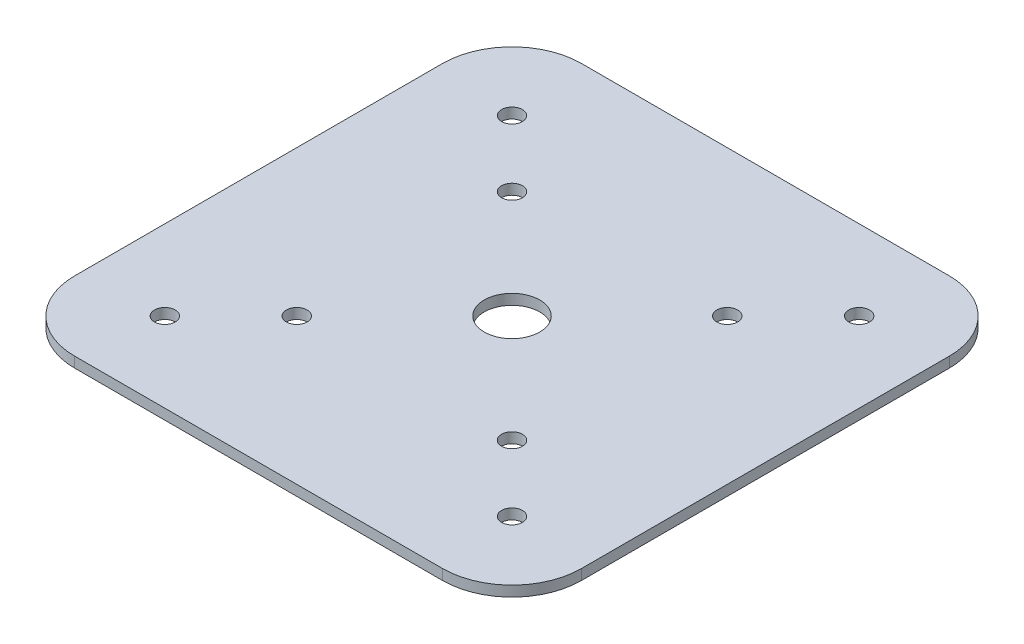
SolidWorks part; units mm, degrees
material "5052-H32"
ref_plane "Front Plane" through (0, 0, 0) normal (0, 0, 1) x (1, 0, 0)
ref_plane "Top Plane" through (0, 0, 0) normal (0, 1, 0) x (1, 0, 0)
ref_plane "Right Plane" through (0, 0, 0) normal (1, 0, 0) x (0, 0, -1)
sketch "Sketch2" plane through (0, 0, 0) normal (0, 1, 0) x (1, 0, 0)
  line L1 (-36.5, 36.5) -> (36.5, 36.5)
  line L2 (-36.5, 36.5) -> (-36.5, -36.5)
  line L3 (-36.5, -36.5) -> (36.5, -36.5)
  line L4 (36.5, 36.5) -> (36.5, -36.5)
  line L5 (-36.5, 36.5) -> (36.5, -36.5) construction
  line L6 (-36.5, -36.5) -> (36.5, 36.5) construction
  circle A0 centre (0, 0) radius 4
  point P0 (0, 0)
  dimension "D2" = 8
  dimension "D1" = 73
extrude "Boss-Extrude1" add sketch "Sketch2" along normal blind 1.5
sketch "Sketch3" plane through (0, 1.5, 0) normal (0, 1, 0) x (1, 0, 0)
  line L1 (-15.5, 15.5) -> (15.5, 15.5) construction
  line L2 (-15.5, 15.5) -> (-15.5, -15.5) construction
  line L3 (-15.5, -15.5) -> (15.5, -15.5) construction
  line L4 (15.5, 15.5) -> (15.5, -15.5) construction
  line L5 (-15.5, 15.5) -> (15.5, -15.5) construction
  line L6 (-15.5, -15.5) -> (15.5, 15.5) construction
  circle A0 centre (-15.5, 15.5) radius 1.5
  circle A1 centre (15.5, 15.5) radius 1.5
  circle A2 centre (15.5, -15.5) radius 1.5
  circle A3 centre (-15.5, -15.5) radius 1.5
  point P0 (0, 0)
  point P6 (0, 0)
  point P16 (0, 0)
  dimension "D2" = 3
  dimension "D1" = 31
  dimension "D3" = 4
extrude "Cut-Extrude1" cut sketch "Sketch3" against normal through all
sketch "Sketch4" plane through (0, 1.5, 0) normal (0, 1, 0) x (1, 0, 0)
  line L1 (-25, 25) -> (25, 25) construction
  line L2 (-25, 25) -> (-25, -25) construction
  line L3 (-25, -25) -> (25, -25) construction
  line L4 (25, 25) -> (25, -25) construction
  line L5 (-25, 25) -> (25, -25) construction
  line L6 (-25, -25) -> (25, 25) construction
  circle A0 centre (-25, 25) radius 1.5
  circle A1 centre (25, 25) radius 1.5
  circle A2 centre (25, -25) radius 1.5
  circle A3 centre (-25, -25) radius 1.5
  point P0 (0, 0)
  point P6 (0, 0)
  point P16 (0, 0)
  dimension "D2" = 3
  dimension "D1" = 50
  dimension "D3" = 4
extrude "Cut-Extrude2" cut sketch "Sketch4" against normal through all
fillet "Fillet1" radius 10 4 edges at (36.5, 0.75, 36.5) (-36.5, 0.75, 36.5) (36.5, 0.75, -36.5) (-36.5, 0.75, -36.5)
